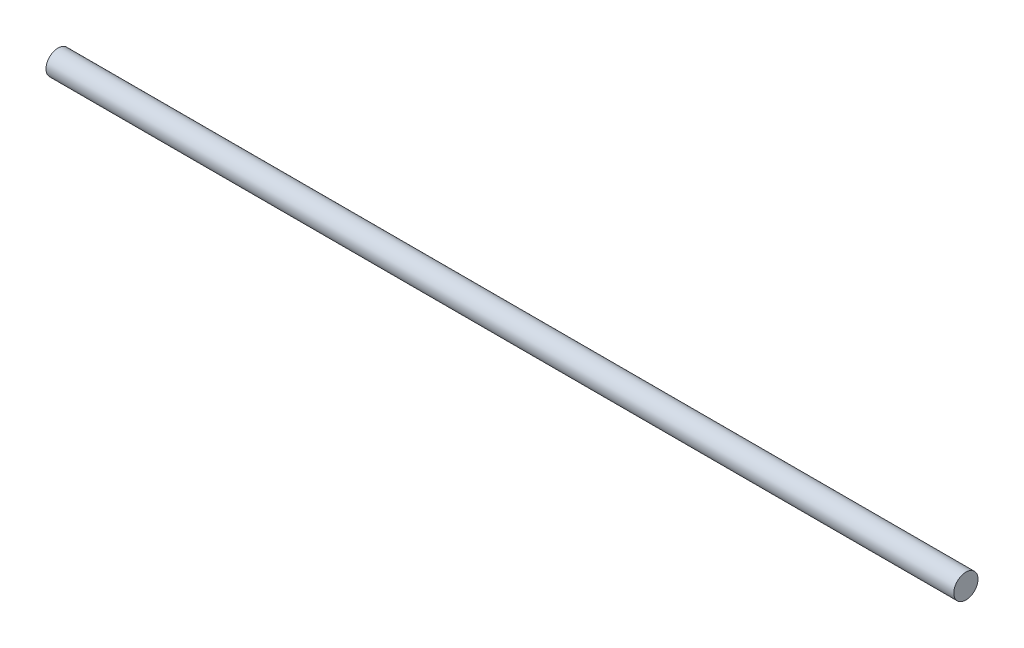
SolidWorks part; units mm, degrees
material "Plain Carbon Steel"
ref_plane "Front Plane" through (0, 0, 0) normal (0, 0, 1) x (1, 0, 0)
ref_plane "Top Plane" through (0, 0, 0) normal (0, 1, 0) x (1, 0, 0)
ref_plane "Right Plane" through (0, 0, 0) normal (1, 0, 0) x (0, 0, -1)
sketch "Sketch1" plane through (0, 0, 0) normal (1, 0, 0) x (0, 0, -1)
  circle A0 centre (0, 0) radius 4
  dimension "D1" = 8
extrude "Boss-Extrude1" add sketch "Sketch1" along normal blind 300
cosmetic thread "Cosmetic Thread1" parameters "D1"=5, "D2"=6.891
cosmetic thread "Cosmetic Thread2" parameters "D1"=5, "D2"=6.891
